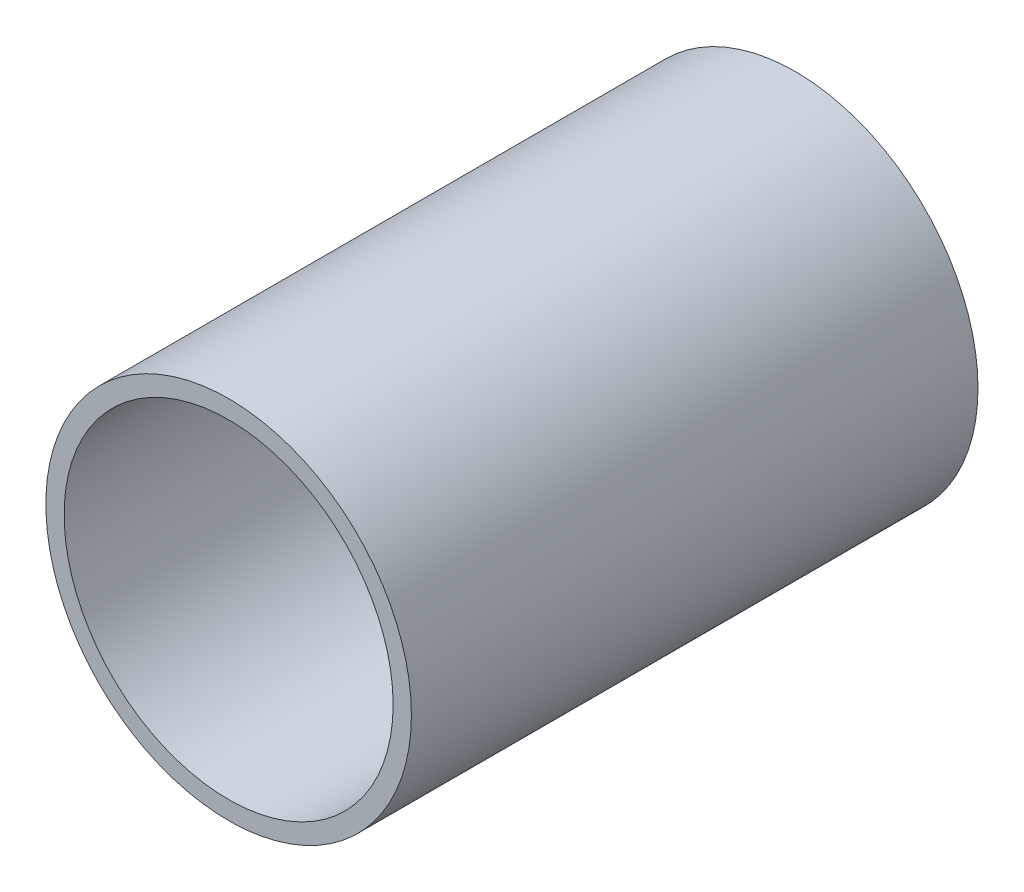
SolidWorks part; units mm, degrees
ref_plane "Front Plane" through (0, 0, 0) normal (0, 0, 1) x (1, 0, 0)
ref_plane "Top Plane" through (0, 0, 0) normal (0, 1, 0) x (1, 0, 0)
ref_plane "Right Plane" through (0, 0, 0) normal (1, 0, 0) x (0, 0, -1)
sketch "Sketch1" plane through (0, 0, 0) normal (0, 0, 1) x (1, 0, 0)
  circle A0 centre (0, 0) radius 9
  circle A1 centre (0, 0) radius 10
  dimension "D1" = 18
  dimension "D2" = 20
extrude "Boss-Extrude1" add sketch "Sketch1" along normal blind 31
